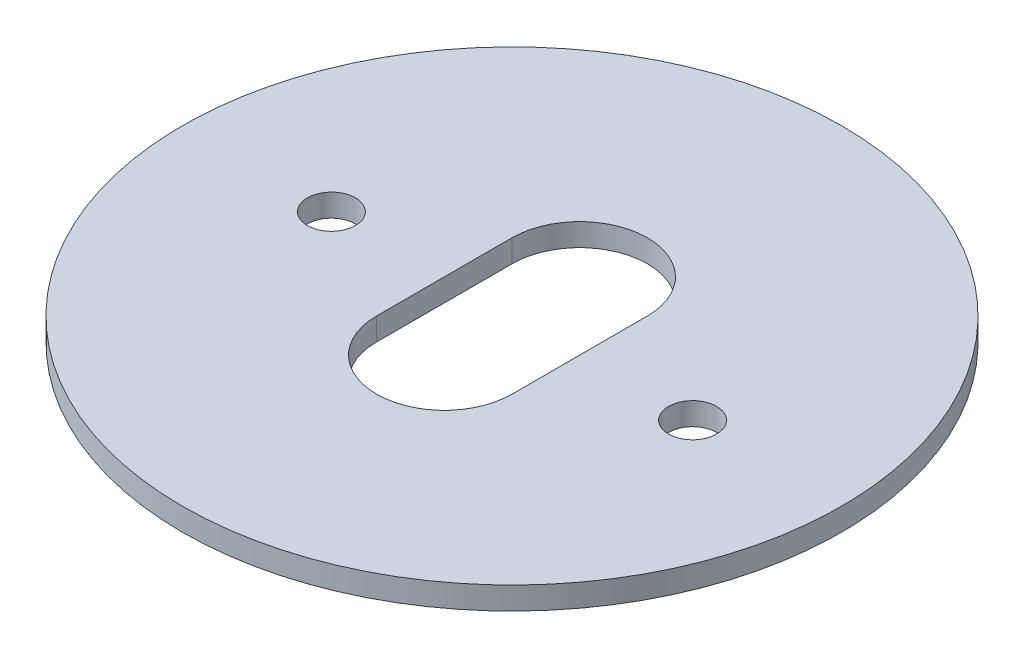
SolidWorks part; units mm, degrees
ref_plane "Front Plane" through (0, 0, 0) normal (0, 0, 1) x (1, 0, 0)
ref_plane "Top Plane" through (0, 0, 0) normal (0, 1, 0) x (1, 0, 0)
ref_plane "Right Plane" through (0, 0, 0) normal (1, 0, 0) x (0, 0, -1)
sketch "Sketch1" plane through (0, 0, 0) normal (0, 1, 0) x (1, 0, 0)
  circle A0 centre (0, 0) radius 46.355
  dimension "D1" = 92.71
extrude "Boss-Extrude1" add sketch "Sketch1" along normal mid plane 3.175
sketch "Sketch2" plane through (0, 1.5875, 0) normal (0, 1, 0) x (1, 0, 0)
  line L0 (-25.4, 0) -> (25.4, 0) construction
  point P0 (-25.4, 0)
  point P1 (25.4, 0)
  point P7 (0, 0)
  point P10 (-25.4, 0)
  point P12 (25.4, 0)
  dimension "D1" = 25.4
hole_wizard "1/4 Clearance Hole1" positions "Sketch2" profile "Sketch3" hole size "1/4" standard "ANSI Inch"
sketch "Sketch3" plane through (25.4, 1.5875, 0) normal (1, 0, 0) x (0, 0, 1)
  line L0 (0, 0) -> (0, 50.8)
  line L1 (0, 50.8) -> (3.3782, 48.7702)
  line L2 (3.3782, 48.7702) -> (3.3782, 0)
  line L5 (3.3782, 0) -> (0, 0)
  line L10 (0, 50.8) -> (-3.3782, 48.7702) construction
  line L11 (0, -6.35) -> (0, 107.95) construction
  dimension "Hole Dia." = 6.7564
  dimension "Hole Depth" = 50.8
  dimension "Drill Angle" = 118
sketch "Sketch4" plane through (0, 1.5875, 0) normal (0, 1, 0) x (1, 0, 0)
  line L0 (0, 9.525) -> (0, -9.525) construction
  line L1 (9.525, 9.525) -> (9.525, -9.525)
  line L2 (-9.525, 9.525) -> (-9.525, -9.525)
  arc A0 (9.525, 9.525) -> (-9.525, 9.525) centre (0, 9.525) ccw
  arc A1 (-9.525, -9.525) -> (9.525, -9.525) centre (0, -9.525) ccw
  point P3 (0, 0)
  point P8 (0, 0)
  dimension "D1" = 19.05
  dimension "D2" = 19.05
extrude "Cut-Extrude1" cut sketch "Sketch4" against normal through all
